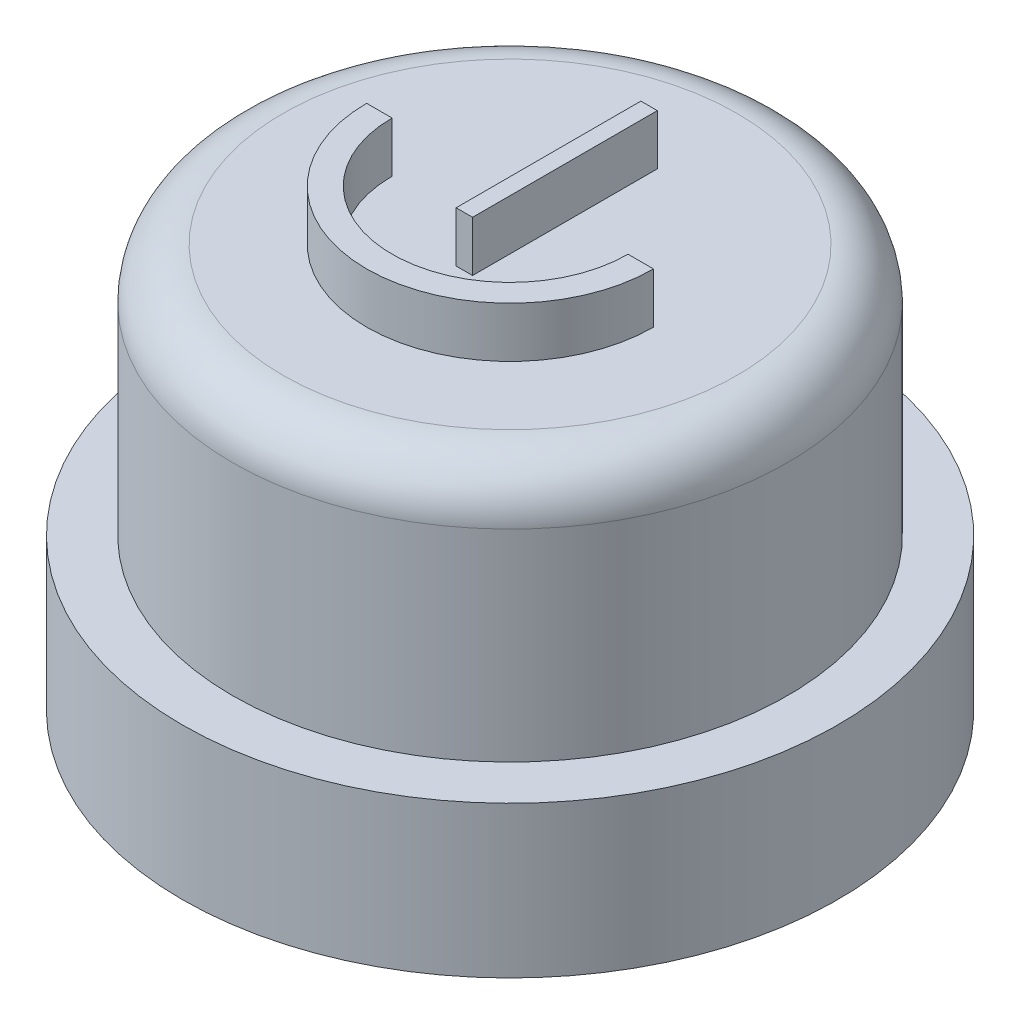
SolidWorks part; units mm, degrees
material "自定义塑料"
ref_plane "前视基准面" through (0, 0, 0) normal (0, 0, 1) x (1, 0, 0)
ref_plane "上视基准面" through (0, 0, 0) normal (0, 1, 0) x (1, 0, 0)
ref_plane "右视基准面" through (0, 0, 0) normal (1, 0, 0) x (0, 0, -1)
other "Configuration Table"
sketch "草图1" plane through (0, 0, 0) normal (0, 1, 0) x (1, 0, 0)
  circle A0 centre (0, 0) radius 6.5
  dimension "D1" = 13
extrude "凸台-拉伸2" add sketch "草图1" along normal blind 3
sketch "草图3" plane through (0, 3, 0) normal (0, 1, 0) x (1, 0, 0)
  circle A0 centre (0, 0) radius 5.5
extrude "凸台-拉伸3" add sketch "草图3" along normal blind 5
fillet "圆角1" radius 1 1 edges at (0, 8, 5.5)
sketch "草图4" plane through (0, 8, 0) normal (0, 1, 0) x (1, 0, 0)
  line L0 (-2.8436, 0) -> (-2.3391, 0)
  line L1 (2.3391, 0) -> (2.8436, 0)
  line L3 (-0.1632, 2.7562) -> (0.1632, 2.7562)
  line L4 (-0.1632, 2.7562) -> (-0.1632, -0.9066)
  line L5 (-0.1632, -0.9066) -> (0.1632, -0.9066)
  line L6 (0.1632, 2.7562) -> (0.1632, -0.9066)
  line L7 (-0.1632, 2.7562) -> (0.1632, -0.9066) construction
  line L8 (-0.1632, -0.9066) -> (0.1632, 2.7562) construction
  arc A0 (-2.8436, 0) -> (2.8436, 0) centre (0, 0) ccw
  arc A1 (-2.3391, 0) -> (2.3391, 0) centre (0, 0) ccw
  point P7 (0, 0.9248)
  point P12 (-2.8413, 0.0059)
extrude "凸台-拉伸4" add sketch "草图4" along normal blind 1
